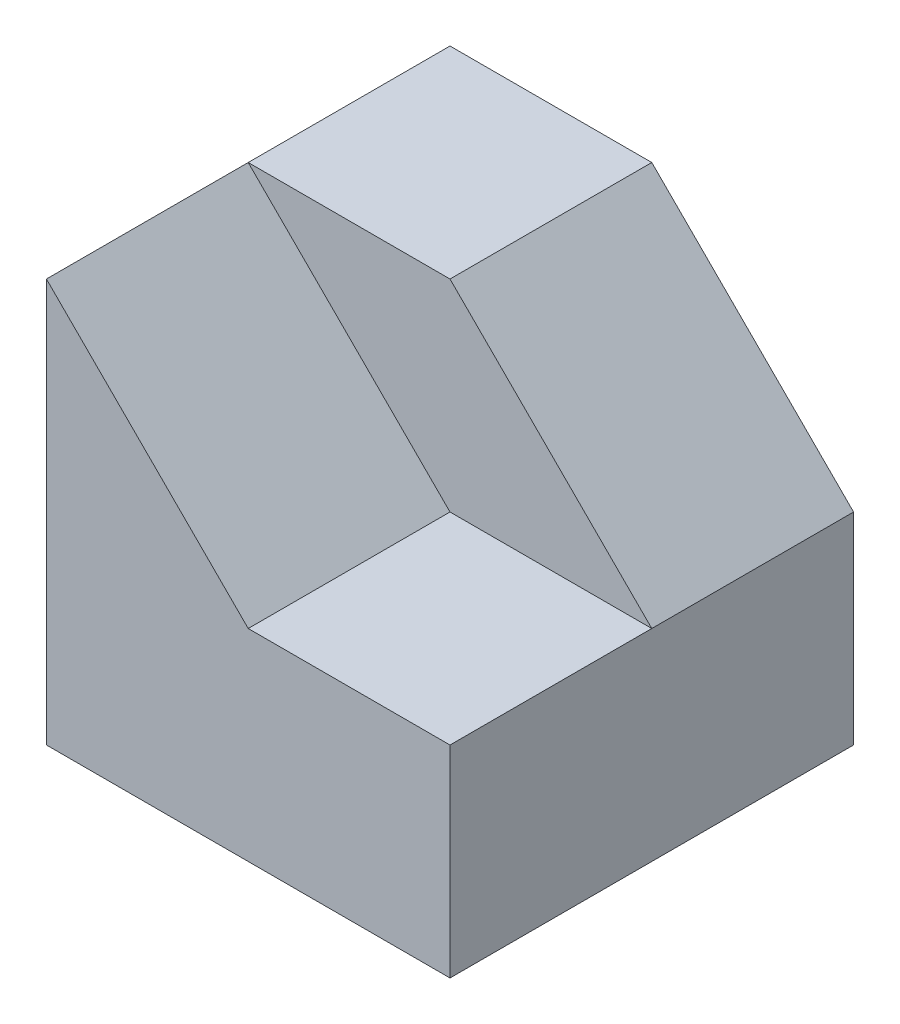
SolidWorks part; units mm, degrees
ref_plane "Alzado" through (0, 0, 0) normal (0, 0, 1) x (1, 0, 0)
ref_plane "Planta" through (0, 0, 0) normal (0, 1, 0) x (1, 0, 0)
ref_plane "Vista lateral" through (0, 0, 0) normal (1, 0, 0) x (0, 0, -1)
sketch "Croquis1" plane through (0, 0, 0) normal (0, 1, 0) x (1, 0, 0)
  line L1 (0, 0) -> (60, 0)
  line L2 (0, 0) -> (0, -60)
  line L3 (0, -60) -> (60, -60)
  line L4 (60, 0) -> (60, -60)
  dimension "D1" = 60
  dimension "D2" = 60
extrude "Saliente-Extruir1" add sketch "Croquis1" along normal blind 60
sketch "Croquis2" plane through (0, 60, 0) normal (0, 1, 0) x (1, 0, 0)
  line L1 (60, -60) -> (30, -60)
  line L2 (60, -60) -> (60, -30)
  line L3 (60, -30) -> (30, -30)
  line L4 (30, -60) -> (30, -30)
  dimension "D1" = 30
  dimension "D2" = 30
extrude "Cortar-Extruir1" cut sketch "Croquis2" against normal blind 30
sketch "Croquis3" plane through (0, 0, 30) normal (0, 0, 1) x (1, 0, 0)
  line L0 (30, 60) -> (60, 30)
  line L1 (60, 30) -> (60, 60)
  line L2 (60, 60) -> (30, 60)
extrude "Cortar-Extruir2" cut sketch "Croquis3" against normal blind 30
sketch "Croquis4" plane through (0, 0, 60) normal (0, 0, 1) x (1, 0, 0)
  line L0 (0, 60) -> (30, 30)
  line L1 (30, 30) -> (30, 60)
  line L2 (30, 60) -> (0, 60)
extrude "Cortar-Extruir3" cut sketch "Croquis4" against normal blind 30
